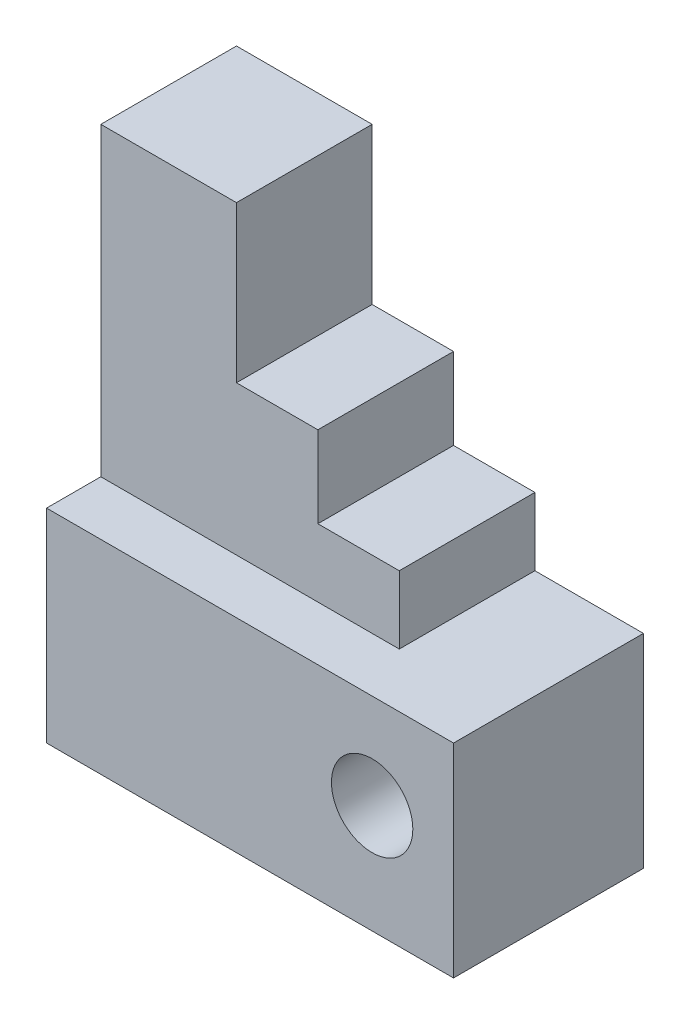
SolidWorks part; units mm, degrees
material "Plain Carbon Steel"
ref_plane "Front Plane" through (0, 0, 0) normal (0, 0, 1) x (1, 0, 0)
ref_plane "Top Plane" through (0, 0, 0) normal (0, 1, 0) x (1, 0, 0)
ref_plane "Right Plane" through (0, 0, 0) normal (1, 0, 0) x (0, 0, -1)
sketch "Sketch1" plane through (0, 0, 0) normal (0, 0, 1) x (1, 0, 0)
  line L0 (0, 30) -> (0, 75)
  line L1 (0, 0) -> (60, 0)
  line L2 (0, 0) -> (0, 30)
  line L3 (0, 30) -> (60, 30)
  line L4 (60, 0) -> (60, 30)
  line L5 (0, 75) -> (20, 75)
  line L6 (20, 75) -> (20, 52)
  line L7 (20, 52) -> (32, 52)
  line L8 (32, 52) -> (32, 40)
  line L9 (32, 40) -> (44, 40)
  line L10 (44, 40) -> (44, 30)
  point P5 (0, 0)
  dimension "D1" = 60
  dimension "D2" = 30
  dimension "D3" = 45
  dimension "D4" = 20
  dimension "D5" = 40
  dimension "D6" = 52
  dimension "D7" = 32
  dimension "D8" = 44
extrude "Boss-Extrude1" add sketch "Sketch1" along normal blind 20 contours L10 L9 L8 L7 L6 L5 L0 L3
sketch "Sketch2" plane through (0, 0, 0) normal (0, 0, -1) x (-1, 0, 0)
  line L1 (0, 0) -> (-60, 0)
  line L2 (0, 0) -> (0, 30)
  line L3 (0, 30) -> (-60, 30)
  line L4 (-60, 0) -> (-60, 30)
  dimension "D1" = 60
  dimension "D2" = 30
extrude "Boss-Extrude2" add sketch "Sketch2" against normal blind 28
sketch "Sketch3" plane through (0, 0, 28) normal (0, 0, 1) x (1, 0, 0)
  circle A0 centre (48, 16) radius 6
  dimension "D1" = 12
  dimension "D2" = 16
  dimension "D3" = 48
extrude "Cut-Extrude1" cut sketch "Sketch3" against normal blind 28
